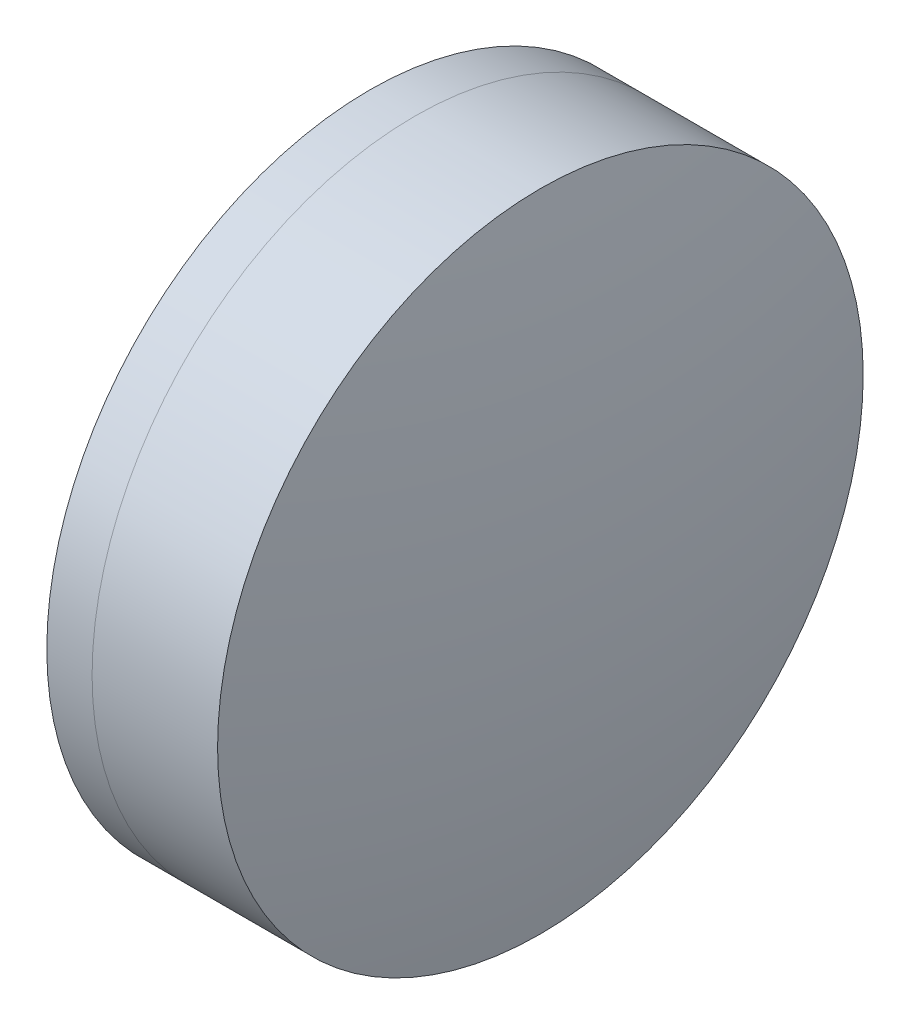
SolidWorks part; units mm, degrees
ref_plane "前视基准面" through (0, 0, 0) normal (0, 0, 1) x (1, 0, 0)
ref_plane "上视基准面" through (0, 0, 0) normal (0, 1, 0) x (1, 0, 0)
ref_plane "右视基准面" through (0, 0, 0) normal (1, 0, 0) x (0, 0, -1)
sketch "草图1" plane through (0, 0, 0) normal (0, 1, 0) x (1, 0, 0)
  line L0 (-9.7026, 0) -> (42.9866, 0) construction
  line L1 (33.1691, -12.5) -> (34.9222, -12.5)
  line L2 (33.1691, 12.5) -> (34.9222, 12.5)
  arc A0 (34.9222, -12.5) -> (34.9222, 12.5) centre (14.8797, 0) ccw
  arc A1 (33.1691, 12.5) -> (33.1691, -12.5) centre (63.5847, 0) ccw
  point P10 (30.7007, 0)
  point P11 (38.5007, 0)
  dimension "D3" = 32.884
  dimension "D4" = 23.621
  dimension "D1" = 12.5
  dimension "D2" = 12.5
  dimension "D5" = 7.8
revolve "旋转1" add sketch "草图1" angle 360 about L0
sketch "草图2" plane through (0, 0, 0) normal (0, 1, 0) x (1, 0, 0)
  line L0 (-0.5519, 0) -> (47.7152, 0) construction
  line L2 (34.9222, 12.5) -> (39.7817, 12.5)
  line L3 (34.9222, -12.5) -> (39.7817, -12.5)
  arc A0 (39.7817, -12.5) -> (39.7817, 12.5) centre (-23.6983, 0) ccw
  arc A1 (34.9222, -12.5) -> (34.9222, 12.5) centre (14.8797, 0) ccw construction
  arc A2 (34.9222, -12.5) -> (34.9222, 12.5) centre (14.8797, 0) ccw
  point P4 (38.5007, 0)
  point P8 (41.0007, 0)
  dimension "D1" = 64.699
  dimension "D2" = 2.5
revolve "旋转3" add sketch "草图2" angle 360 about L0
